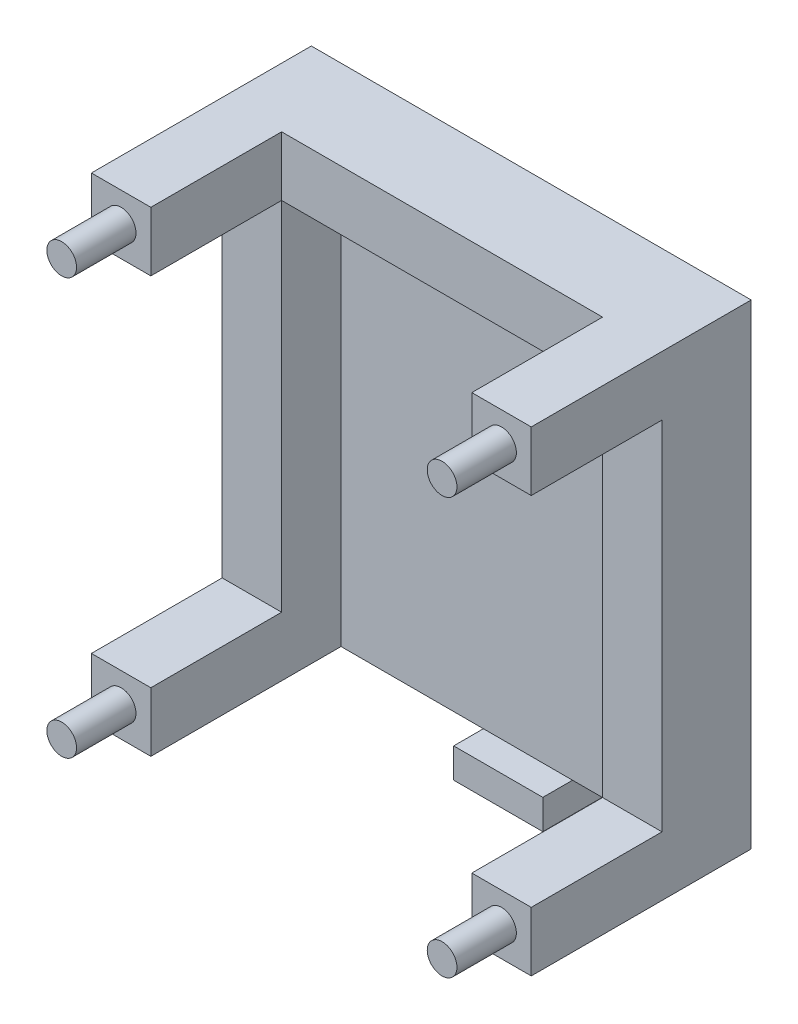
SolidWorks part; units mm, degrees
ref_plane "Alzado" through (0, 0, 0) normal (0, 0, 1) x (1, 0, 0)
ref_plane "Planta" through (0, 0, 0) normal (0, 1, 0) x (1, 0, 0)
ref_plane "Vista lateral" through (0, 0, 0) normal (1, 0, 0) x (0, 0, -1)
sketch "Croquis1" plane through (0, 0, 0) normal (0, 0, 1) x (1, 0, 0)
  line L0 (1.4005, 36.5086) -> (55.4005, 36.5086)
  line L1 (55.4005, 36.5086) -> (55.4005, -33.4914)
  line L2 (55.4005, -33.4914) -> (1.4005, -33.4914)
  line L3 (1.4005, -33.4914) -> (1.4005, 36.5086)
  dimension "D1" = 54
  dimension "D2" = 70
extrude "Saliente-Extruir1" add sketch "Croquis1" along normal blind 5
sketch "Croquis2" plane through (0, 0, 5) normal (0, 0, 1) x (1, 0, 0)
  line L0 (1.4005, 36.5086) -> (-8.0995, 36.5086)
  line L1 (55.4005, 36.5086) -> (1.4005, 36.5086) construction
  line L2 (55.4005, 36.5086) -> (1.4005, 36.5086)
  line L3 (1.4005, 36.5086) -> (1.4005, -33.4914)
  line L4 (1.4005, -33.4914) -> (55.4005, -33.4914) construction
  line L5 (1.4005, -33.4914) -> (-8.0995, -33.4914)
  line L6 (-8.0995, -33.4914) -> (-8.0995, 36.5086)
  line L7 (1.4005, 36.5086) -> (-8.0995, 36.5086)
sketch "Croquis4" plane through (0, 0, 0) normal (0, 0, -1) x (-1, 0, 0)
  line L0 (-55.4005, 36.5086) -> (-55.4005, 46.5086)
  line L1 (-55.4005, 46.5086) -> (-1.4005, 46.5086)
  line L2 (-1.4005, 46.5086) -> (-1.4005, 36.5086)
  line L3 (-1.4005, 36.5086) -> (-55.4005, 36.5086)
  dimension "D1" = 10
extrude "Saliente-Extruir5" add sketch "Croquis4" against normal blind 15
sketch "Croquis5" plane through (0, 0, 0) normal (0, 0, -1) x (-1, 0, 0)
  line L0 (-55.4005, 46.5086) -> (-65.4005, 46.5086)
  line L1 (-65.4005, 46.5086) -> (-65.4005, 36.5086)
  line L2 (-65.4005, 36.5086) -> (-55.4005, 36.5086)
  line L3 (-55.4005, 36.5086) -> (-55.4005, 46.5086)
  line L4 (-55.4005, 46.5086) -> (-28.4005, 46.5086)
  line L5 (-1.4005, 46.5086) -> (-55.4005, 46.5086) construction
  line L6 (-28.4005, 46.5086) -> (-28.4005, 24.5969)
  line L7 (-55.4005, -33.4914) -> (-65.4005, -33.4914)
  line L8 (-65.4005, -33.4914) -> (-65.4005, -23.4914)
  line L9 (-65.4005, -23.4914) -> (-55.4005, -23.4914)
  line L10 (-55.4005, -33.4914) -> (-55.4005, 46.5086) construction
  line L11 (-55.4005, -23.4914) -> (-55.4005, -33.4914)
  line L12 (-55.4005, -33.4914) -> (-55.597, -33.6261)
  line L13 (-1.4005, -23.4914) -> (-1.4005, -33.4914)
  line L14 (8.5995, -23.4914) -> (-1.4005, -23.4914)
  line L15 (8.5995, -33.4914) -> (8.5995, -23.4914)
  line L16 (-1.4005, -33.4914) -> (8.5995, -33.4914)
  line L17 (-1.4005, 36.5086) -> (-1.4005, 46.5086)
  line L18 (8.5995, 36.5086) -> (-1.4005, 36.5086)
  line L19 (8.5995, 46.5086) -> (8.5995, 36.5086)
  line L20 (-1.4005, 46.5086) -> (8.5995, 46.5086)
  line L21 (-1.4005, -33.4914) -> (-1.2041, -33.6261)
  line M1 (-1.4005, -33.4914) -> (-1.4005, 46.5086)
  line M3 (-55.4005, 46.5086) -> (-55.4005, -33.4914)
extrude "Saliente-Extruir6" add sketch "Croquis5" against normal blind 37 contours L1 L2 L0 M3 | L9 L8 L7 M3 | L16 L15 L14 M1 | L20 L18 L19 M1
sketch "Croquis6" plane through (0, 0, 0) normal (0, 0, -1) x (-1, 0, 0)
  line L1 (8.5995, -33.4914) -> (-65.4005, -33.4914) construction
  line L3 (-40.349, -38.4914) -> (-40.349, -33.4914)
  line L4 (-40.349, -33.4914) -> (-25.349, -33.4914)
  line L5 (-25.349, -33.4914) -> (-25.349, -38.4914)
  line L6 (-25.349, -38.4914) -> (-40.349, -38.4914)
  dimension "D1" = 5
  dimension "D4" = 15
extrude "Saliente-Extruir7" add sketch "Croquis6" against normal blind 10 separate body
sketch "Croquis8" plane through (0, 0, 0) normal (0, 0, -1) x (-1, 0, 0)
  line L0 (-65.4005, 36.5086) -> (-65.4005, -23.4914)
  line L1 (-65.4005, -23.4914) -> (-55.4005, -23.4914)
  line L2 (-55.4005, -23.4914) -> (-55.4005, 36.5086)
  line L3 (-55.4005, 36.5086) -> (-65.4005, 36.5086)
  line L4 (-28.4005, 46.5086) -> (-28.4005, 34.2655)
  line L5 (8.5995, 46.5086) -> (-65.4005, 46.5086) construction
  line L6 (-1.4005, 36.5086) -> (8.5995, 36.5086)
  line L7 (-1.4005, -23.4914) -> (-1.4005, 36.5086)
  line L8 (8.5995, -23.4914) -> (-1.4005, -23.4914)
  line L9 (8.5995, 36.5086) -> (8.5995, -23.4914)
  line M1 (-1.4005, -23.4914) -> (-1.4005, 36.5086)
  line M2 (-1.4005, 36.5086) -> (8.5995, 36.5086)
  line M6 (-65.4005, 36.5086) -> (-55.4005, 36.5086)
  line M7 (-55.4005, 36.5086) -> (-55.4005, -23.4914)
  line M8 (-55.4005, -23.4914) -> (-65.4005, -23.4914)
  line M12 (8.5995, -23.4914) -> (-1.4005, -23.4914)
extrude "Saliente-Extruir9" add sketch "Croquis8" against normal blind 15 contours L0 M6 M8 M7 | L9 M2 M1 M12
sketch "Croquis9" plane through (0, 0, 37) normal (0, 0, 1) x (1, 0, 0)
  line L0 (-8.5995, 46.5086) -> (-8.5995, 36.5086)
  line L1 (-8.5995, 46.5086) -> (-8.5995, 36.5086) construction
  line L2 (-8.5995, 41.5086) -> (1.4005, 41.5086)
  line L3 (1.4005, 36.5086) -> (1.4005, 46.5086) construction
  line L4 (-8.5995, 46.5086) -> (-8.5995, 6.5086)
  line L5 (-8.5995, 36.5086) -> (-8.5995, -23.4914) construction
  line L6 (-8.5995, 6.5086) -> (65.4005, 6.5086)
  line L7 (65.4005, 36.5086) -> (65.4005, -23.4914) construction
  line L8 (65.4005, 6.5086) -> (28.4005, 6.5086)
  line L9 (28.4005, 6.5086) -> (28.4005, 19.0549)
  circle A0 centre (-3.5995, 41.5086) radius 2.5
  circle A1 centre (60.4005, 41.5086) radius 2.5
  circle A2 centre (60.4005, -28.4914) radius 2.5
  circle A3 centre (-3.5995, -28.4914) radius 2.5
  dimension "D1" = 5
extrude "Saliente-Extruir10" add sketch "Croquis9" along normal blind 10 contours L2 A0 | L2 A0 | A1 | A2 | A3
sketch "Croquis11" plane through (0, 0, 0) normal (0, 0, -1) x (-1, 0, 0)
  line L0 (-65.4005, 46.5086) -> (-65.4005, 36.5086)
  line L1 (-65.4005, 36.5086) -> (-65.4005, 41.5086)
  line L2 (-65.4005, 41.5086) -> (-60.4005, 41.5086)
  line L3 (-60.4005, 41.5086) -> (8.5995, 41.5086)
  line L4 (8.5995, -33.4914) -> (8.5995, 46.5086) construction
  line L5 (8.5995, 41.5086) -> (-25.9005, 41.5086)
  line L6 (-65.4005, 46.5086) -> (-65.4005, 6.5086)
  line L7 (-65.4005, 46.5086) -> (-65.4005, -33.4914) construction
  line L8 (-65.4005, 6.5086) -> (-25.349, 6.5086)
  line L9 (-25.349, 6.5086) -> (8.5995, 6.5086)
  line L10 (-65.4005, -33.4914) -> (-28.4005, -33.4914)
  line L12 (8.5995, -33.4914) -> (-65.4005, -33.4914) construction
  line L13 (-28.4005, -33.4914) -> (-28.4005, 6.5086)
  circle A0 centre (-60.4005, 41.5086) radius 2.55
  circle A1 centre (-60.4005, -28.4914) radius 2.55
  circle A2 centre (3.5995, -28.4914) radius 2.55
  circle A3 centre (3.5995, 41.5086) radius 2.55
  dimension "D1" = 40.0516
  dimension "D2" = 5.1
extrude "Cortar-Extruir1" cut sketch "Croquis11" against normal blind 10 contours L3 A0 L2 | L2 A0 L3 | A3 L5 | A3 L5 | A2 | A1
